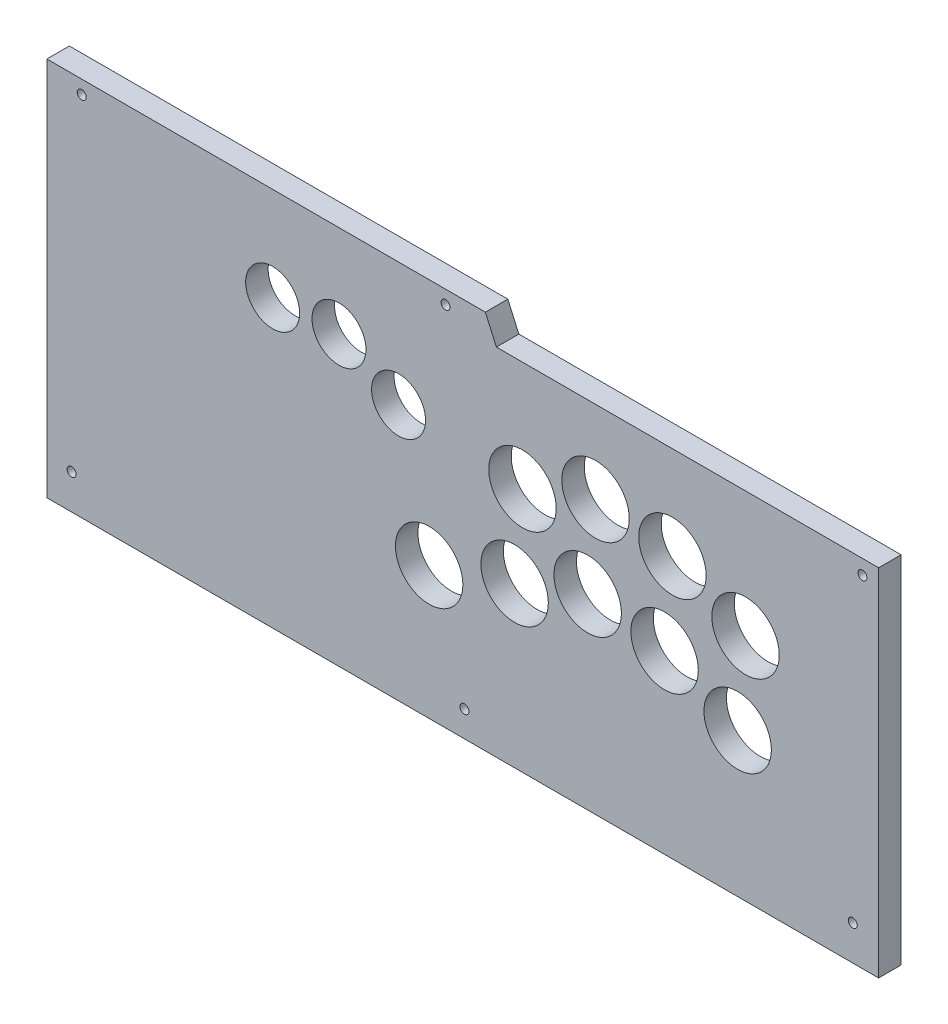
SolidWorks part; units mm, degrees
ref_plane "Front Plane" through (0, 0, 0) normal (0, 0, 1) x (1, 0, 0)
ref_plane "Top Plane" through (0, 0, 0) normal (0, 1, 0) x (1, 0, 0)
ref_plane "Right Plane" through (0, 0, 0) normal (1, 0, 0) x (0, 0, -1)
sketch "Sketch1" plane through (0, 0, 0) normal (0, 0, 1) x (1, 0, 0)
  line L0 (-184.95, 0) -> (184.95, 0)
  line L5 (184.95, 0) -> (184.95, 158)
  line L6 (184.95, 158) -> (14.95, 158)
  line L7 (14.95, 158) -> (10.05, 169)
  line L8 (10.05, 169) -> (-184.95, 169)
  line L9 (-184.95, 169) -> (-184.95, 0)
  point P3 (0, 0)
  dimension "D1" = 369.9
  dimension "D2" = 158
  dimension "D3" = 170
  dimension "D4" = 195
  dimension "D5" = 169
sketch "Sketch2" plane through (0, 0, 0) normal (0, 0, 1) x (1, 0, 0)
  line L0 (10.05, 169) -> (10.05, 0) construction
  line L1 (-184.95, 0) -> (184.95, 0) construction
  line L3 (184.95, 158) -> (14.95, 158) construction
  circle A0 centre (23.05, 71) radius 15
  circle A1 centre (55.55, 83.2) radius 15
  circle A2 centre (89.75, 78.4) radius 15
  circle A3 centre (122.25, 64) radius 15
  circle A12 centre (26.55, 109.2) radius 15
  circle A13 centre (59.05, 121.4) radius 15
  circle A14 centre (93.25, 116.6) radius 15
  circle A15 centre (125.75, 102.2) radius 15
  circle A17 centre (-14.95, 59) radius 15
  circle A18 centre (-28.55, 114) radius 12
  circle A19 centre (-55.05, 128) radius 12
  circle A20 centre (-84.55, 127.3) radius 12
  circle A21 centre (-7.65, 163) radius 2
  circle A22 centre (-169.45, 163) radius 2
  circle A23 centre (-173.95, 15.5) radius 2
  circle A24 centre (0.75, 11.5) radius 2
  circle A25 centre (173.45, 15.5) radius 2
  circle A26 centre (177.75, 151.5) radius 2
  dimension "D2" = 30
  dimension "D13" = 25
  dimension "D15" = 55
  dimension "D17" = 26.5
  dimension "D19" = 29.5
  dimension "D21" = 17.7
  dimension "D23" = 6
  dimension "D25" = 11
  dimension "D27" = 9.3
  dimension "D29" = 15.5
  dimension "D31" = 7.2
  dimension "D1" = 13
  dimension "D3" = 87
  dimension "D4" = 32.5
  dimension "D5" = 12.2
  dimension "D6" = 34.2
  dimension "D7" = 32.5
  dimension "D8" = 7.4
  dimension "D9" = 7
  dimension "D11" = 38.2
  dimension "D12" = 3.5
  dimension "D14" = 110
  dimension "D16" = 38.6
  dimension "D18" = 14
  dimension "D20" = 0.7
  dimension "D22" = 6
  dimension "D24" = 15.5
  dimension "D26" = 15.5
  dimension "D28" = 11.5
  dimension "D30" = 11.5
  dimension "D32" = 6.5
  dimension "D10" = 2
extrude "Boss-Extrude1" add sketch "Sketch1" along normal mid plane 10
extrude "Cut-Extrude1" cut sketch "Sketch2" against normal through all both and the other way through all
